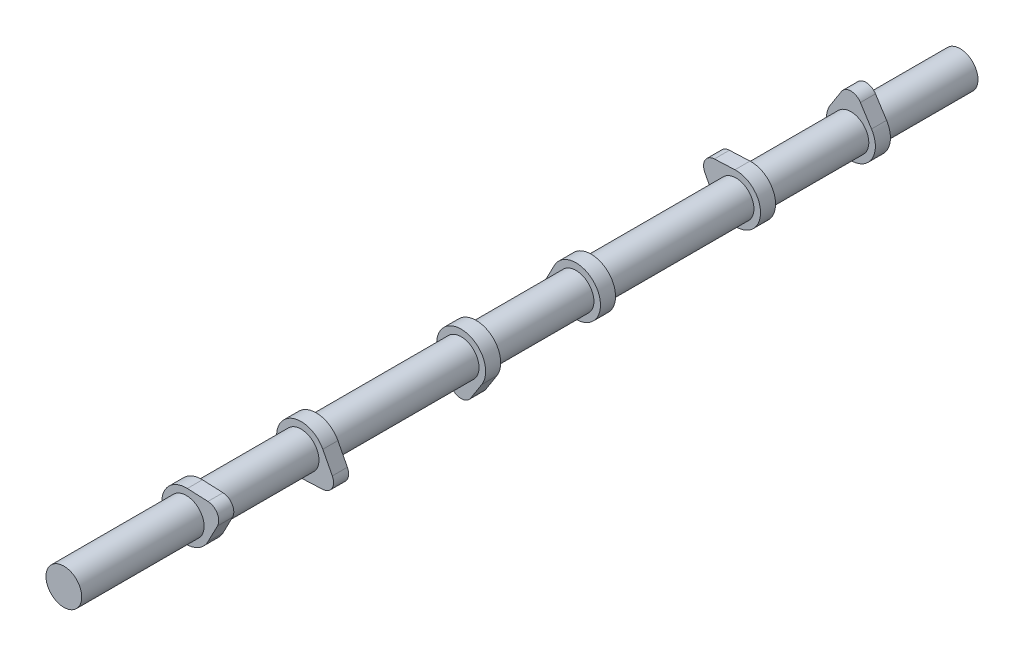
SolidWorks part; units mm, degrees
ref_plane "Front Plane" through (0, 0, 0) normal (0, 0, 1) x (1, 0, 0)
ref_plane "Top Plane" through (0, 0, 0) normal (0, 1, 0) x (1, 0, 0)
ref_plane "Right Plane" through (0, 0, 0) normal (1, 0, 0) x (0, 0, -1)
sketch "Sketch1" plane through (0, 0, 0) normal (0, 0, 1) x (1, 0, 0)
  circle A0 centre (0, 0) radius 9.5
extrude "Boss-Extrude1" add sketch "Sketch1" along normal blind 476
ref_plane "Plane1" through (0, 0, 50) normal (0, 0, -1) x (-1, 0, 0)
sketch "Sketch2" plane through (0, 0, 50) normal (0, 0, -1) x (-1, 0, 0)
  line L0 (-10.9545, 7) -> (-5.0559, 16.2308)
  line L1 (5.0559, 16.2308) -> (10.9545, 7)
  arc A0 (-10.9545, 7) -> (10.9545, 7) centre (0, 0) ccw
  arc A1 (5.0559, 16.2308) -> (-5.0559, 16.2308) centre (0, 13) ccw
  dimension "D1" = 13
extrude "Boss-Extrude2" add sketch "Sketch2" against normal blind 8
ref_plane "Plane2" through (0, 0, 111) normal (0, 0, 1) x (1, 0, 0)
sketch "Sketch3" plane through (0, 0, 111) normal (0, 0, 1) x (1, 0, 0)
  line L4 (-0.585, 12.9868) -> (-11.5283, 12.4939)
  line L5 (-16.5842, 3.7368) -> (-11.5394, -5.9868)
  arc A4 (-11.5394, -5.9868) -> (-0.585, 12.9868) centre (0, 0) ccw
  arc A5 (-11.5283, 12.4939) -> (-16.5842, 3.7368) centre (-11.2583, 6.5) ccw
extrude "Boss-Extrude3" add sketch "Sketch3" along normal blind 8
ref_plane "Plane3" through (0, 0, 196) normal (0, 0, 1) x (1, 0, 0)
sketch "Sketch4" plane through (0, 0, 196) normal (0, 0, 1) x (1, 0, 0)
  line L4 (-11.5394, 5.9868) -> (-16.5842, -3.7368)
  line L5 (-11.5283, -12.4939) -> (-0.585, -12.9868)
  arc A4 (-0.585, -12.9868) -> (-11.5394, 5.9868) centre (0, 0) ccw
  arc A5 (-16.5842, -3.7368) -> (-11.5283, -12.4939) centre (-11.2583, -6.5) ccw
ref_plane "Plane4" through (0, 0, 257) normal (0, 0, 1) x (1, 0, 0)
sketch "Sketch5" plane through (0, 0, 257) normal (0, 0, 1) x (1, 0, 0)
  line L4 (-10.9545, -7) -> (-5.0559, -16.2308)
  line L5 (5.0559, -16.2308) -> (10.9545, -7)
  arc A4 (10.9545, -7) -> (-10.9545, -7) centre (0, 0) ccw
  arc A5 (-5.0559, -16.2308) -> (5.0559, -16.2308) centre (0, -13) ccw
ref_plane "Plane5" through (0, 0, 342) normal (0, 0, 1) x (1, 0, 0)
sketch "Sketch6" plane through (0, 0, 342) normal (0, 0, 1) x (1, 0, 0)
  line L4 (0.585, -12.9868) -> (11.5283, -12.4939)
  line L5 (16.5842, -3.7368) -> (11.5394, 5.9868)
  arc A4 (11.5394, 5.9868) -> (0.585, -12.9868) centre (0, 0) ccw
  arc A5 (11.5283, -12.4939) -> (16.5842, -3.7368) centre (11.2583, -6.5) ccw
ref_plane "Plane6" through (0, 0, 403) normal (0, 0, 1) x (1, 0, 0)
sketch "Sketch7" plane through (0, 0, 403) normal (0, 0, 1) x (1, 0, 0)
  line L4 (11.5394, -5.9868) -> (16.5842, 3.7368)
  line L5 (11.5283, 12.4939) -> (0.585, 12.9868)
  arc A4 (0.585, 12.9868) -> (11.5394, -5.9868) centre (0, 0) ccw
  arc A5 (16.5842, 3.7368) -> (11.5283, 12.4939) centre (11.2583, 6.5) ccw
extrude "Boss-Extrude4" add sketch "Sketch4" along normal blind 8
extrude "Boss-Extrude5" add sketch "Sketch5" along normal blind 8
extrude "Boss-Extrude6" add sketch "Sketch6" along normal blind 8
extrude "Boss-Extrude7" add sketch "Sketch7" along normal blind 8
